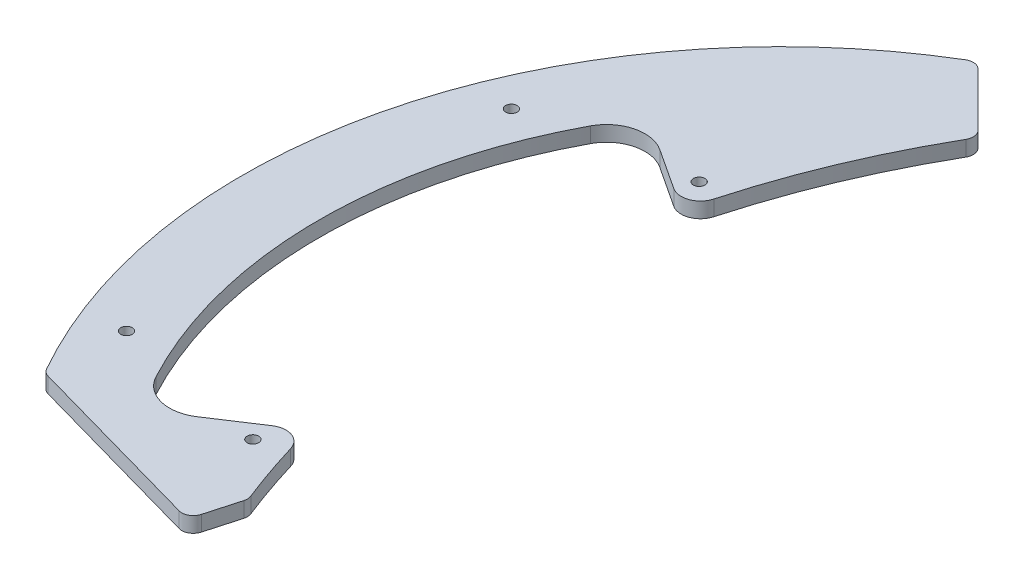
SolidWorks part; units mm, degrees
material "PMMA"
ref_plane "Front Plane" through (0, 0, 0) normal (0, 0, 1) x (1, 0, 0)
ref_plane "Top Plane" through (0, 0, 0) normal (0, 1, 0) x (1, 0, 0)
ref_plane "Right Plane" through (0, 0, 0) normal (1, 0, 0) x (0, 0, -1)
sketch "Sketch1" plane through (0, 0, 0) normal (0, 1, 0) x (1, 0, 0)
  circle A0 centre (0, 0) radius 140
  dimension "D1" = 280
extrude "Boss-Extrude1" add sketch "Sketch1" along normal blind 4
sketch "Sketch17" plane through (0, 0, 0) normal (0, -1, 0) x (1, 0, 0)
  line L0 (-50, 90) -> (-121.2436, 70)
  line L1 (-50, 90) -> (50, 90)
  line L2 (-121.2436, 70) -> (-121.2436, 140)
  line L3 (-121.2436, 140) -> (121.2436, 140)
  line L4 (121.2436, 140) -> (121.2436, 70)
  line L5 (121.2436, 70) -> (50, 90)
  circle A0 centre (0, 0) radius 140 construction
  dimension "D1" = 90
  dimension "D2" = 50
  dimension "D3" = 50
  dimension "D4" = 70
extrude "Cut-Extrude1" cut sketch "Sketch17" against normal up to next
sketch "Sketch19" plane through (0, 4, 0) normal (0, 1, 0) x (1, 0, 0)
  line L0 (-68.5894, 68.5894) -> (68.5894, -68.5894) construction
  line L1 (97, 40.1787) -> (40.1787, 97) construction
  line L2 (40.1787, 97) -> (-40.1787, 97) construction
  line L3 (-40.1787, 97) -> (-97, 40.1787) construction
  line L4 (-97, 40.1787) -> (-97, -40.1787) construction
  line L5 (-97, -40.1787) -> (-40.1787, -97) construction
  line L6 (-40.1787, -97) -> (40.1787, -97) construction
  line L7 (40.1787, -97) -> (97, -40.1787) construction
  line L8 (97, -40.1787) -> (97, 40.1787) construction
  line L9 (68.5894, 68.5894) -> (-68.5894, -68.5894) construction
  circle A0 centre (-79.196, -57.9828) radius 1.5
  circle A1 centre (-79.196, 57.9828) radius 1.5
  circle A2 centre (79.196, 57.9828) radius 1.5
  circle A3 centre (79.196, -57.9828) radius 1.5
  circle A4 centre (0, 0) radius 97 construction
  circle A5 centre (-57.9828, 79.196) radius 1.5
  circle A6 centre (57.9828, 79.196) radius 1.5
  circle A7 centre (57.9828, -79.196) radius 1.5
  circle A8 centre (-57.9828, -79.196) radius 1.5
  dimension "D5" = 3
  dimension "D1" = 15
  dimension "D6" = 97
extrude "Cut-Extrude3" cut sketch "Sketch19" against normal up to next
sketch "Sketch20" plane through (0, 4, 0) normal (0, 1, 0) x (1, 0, 0)
  line L0 (-70, 121.2436) -> (-50, 101.2436)
  line L1 (-50, 101.2436) -> (50, 101.2436)
  line L2 (50, 101.2436) -> (70, 121.2436)
  arc A1 (121.2436, -70) -> (-121.2436, -70) centre (0, 0) ccw construction
  dimension "D1" = 140
  dimension "D2" = 100
  dimension "D3" = 50
extrude "Cut-Extrude4" cut sketch "Sketch20" against normal up to next
sketch "Sketch21" plane through (0, 4, 0) normal (0, 1, 0) x (1, 0, 0)
  line L0 (-52.1633, 87.3282) -> (0, 50)
  line L1 (0, 50) -> (52.1633, 87.3282)
  line L2 (66.2648, 73.5916) -> (30, 20)
  line L3 (30, 20) -> (67.2983, -75.56)
  line L4 (49.6537, -84.7301) -> (0, -10) construction
  line L5 (0, -10) -> (-49.6537, -84.7301) construction
  line L6 (-67.2983, -75.56) -> (-30, 20)
  line L7 (-30, 20) -> (-66.2648, 73.5916)
  line L8 (-67.2983, -75.56) -> (-72.9344, -90)
  line L9 (-72.9344, -90) -> (72.9344, -90)
  line L10 (72.9344, -90) -> (67.2983, -75.56)
  line L11 (-50, -90) -> (50, -90) construction
  line L12 (-68.5894, 68.5894) -> (68.5894, -68.5894) construction
  line L13 (97, 40.1787) -> (40.1787, 97) construction
  line L14 (40.1787, 97) -> (-40.1787, 97) construction
  line L15 (-40.1787, 97) -> (-97, 40.1787) construction
  line L16 (-97, 40.1787) -> (-97, -40.1787) construction
  line L17 (-97, -40.1787) -> (-40.1787, -97) construction
  line L18 (-40.1787, -97) -> (40.1787, -97) construction
  line L19 (40.1787, -97) -> (97, -40.1787) construction
  line L20 (97, -40.1787) -> (97, 40.1787) construction
  line L21 (68.5894, 68.5894) -> (-68.5894, -68.5894) construction
  arc A0 (-66.2648, 73.5916) -> (-52.1633, 87.3282) centre (-57.9828, 79.196) cw
  arc A1 (66.2648, 73.5916) -> (52.1633, 87.3282) centre (57.9828, 79.196) ccw
  arc A2 (-49.6537, -84.7301) -> (-67.2983, -75.56) centre (-57.9828, -79.196) cw construction
  arc A3 (67.2983, -75.56) -> (49.6537, -84.7301) centre (57.9828, -79.196) cw construction
  circle A5 centre (0, 0) radius 97 construction
  dimension "D2" = 10
  dimension "D3" = 15
  dimension "D8" = 97
extrude "Cut-Extrude5" [suppressed] cut sketch "Sketch21" against normal up to next
fillet "Fillet1" [suppressed] radius 20
fillet "Fillet2" radius 10 2 edges at (50, 2, -101.2436) (-50, 2, -101.2436)
sketch "Sketch22" plane through (0, 4, 0) normal (0, 1, 0) x (1, 0, 0)
  line L1 (85, 24) -> (118, 24)
  line L2 (85, 24) -> (85, -24)
  line L3 (85, -24) -> (118, -24)
  line L4 (118, 24) -> (118, -24)
  line L5 (-118, 26) -> (-85, 26)
  line L6 (-118, 26) -> (-118, -27)
  line L7 (-118, -27) -> (-85, -27)
  line L8 (-85, 26) -> (-85, -27)
  dimension "D1" = 85
  dimension "D2" = 85
  dimension "D3" = 48
  dimension "D4" = 53
  dimension "D5" = 33
  dimension "D6" = 33
  dimension "D7" = 26
  dimension "D8" = 24
extrude "Cut-Extrude6" [suppressed] cut sketch "Sketch22" against normal up to next
fillet "Fillet3" [suppressed] radius 3
sketch "Sketch23" plane through (0, 4, 0) normal (0, 1, 0) x (1, 0, 0)
  line L0 (-66.3365, -71.9548) -> (-73.1897, -96.3671)
  line L1 (-70, 121.2436) -> (-52.9289, 104.1725) construction
  line L2 (-121.2436, -70) -> (-50, -90) construction
  arc A0 (-52.9289, 104.1725) -> (-66.3365, -71.9548) centre (119.2928, 2.4883) ccw
  arc A3 (-66.3365, -71.9548) -> (-52.9289, -99.196) centre (119.2928, 2.4883) ccw construction
  circle A4 centre (-57.9828, -79.196) radius 1.5 construction
  dimension "D2" = 20
  dimension "D3" = 200
  dimension "D4" = 90
  dimension "D5" = 10
extrude "Cut-Extrude8" cut sketch "Sketch23" against normal through all and the other way through all
sketch "Sketch24" plane through (0, 4, 0) normal (0, 1, 0) x (1, 0, 0)
  line L0 (0, 0) -> (-100.309, 65.8643)
  line L1 (-100.309, -65.8643) -> (0, 0)
  arc A0 (-100.309, 65.8643) -> (-100.309, -65.8643) centre (0, 0) ccw
  circle A1 centre (-79.196, 57.9828) radius 1.5 construction
  circle A2 centre (-79.196, -57.9828) radius 1.5 construction
  arc A3 (-70, 121.2436) -> (-121.2436, -70) centre (0, 0) ccw construction
  dimension "D2" = 5
  dimension "D3" = 20
  dimension "D1" = 5
extrude "Cut-Extrude9" cut sketch "Sketch24" against normal up to next
fillet "Fillet4" radius 5 2 edges at (-74.0638, 2, 48.6314) (-75.1422, 2, -49.3395)
fillet "Fillet6" radius 10 2 edges at (-100.309, 2, -65.8643) (-100.309, 2, 65.8643)
sketch "Sketch25" plane through (0, 4, 0) normal (0, 1, 0) x (1, 0, 0)
  circle A0 centre (-120, 50) radius 1.5
  circle A1 centre (-120, -50) radius 1.5
  dimension "D1" = 3
  dimension "D2" = 50
  dimension "D3" = 50
  dimension "D4" = 120
extrude "Cut-Extrude10" cut sketch "Sketch25" against normal up to next
fillet "Fillet5" radius 3 5 edges at (-70, 2, -121.2436) (-66.3365, 2, 71.9548) (-69.8389, 2, 84.4307) (-121.2436, 2, 70) (-52.9289, 2, -104.1725)
equation "\"D3@Sketch20\" = \"D2@Sketch20\" / 2"
